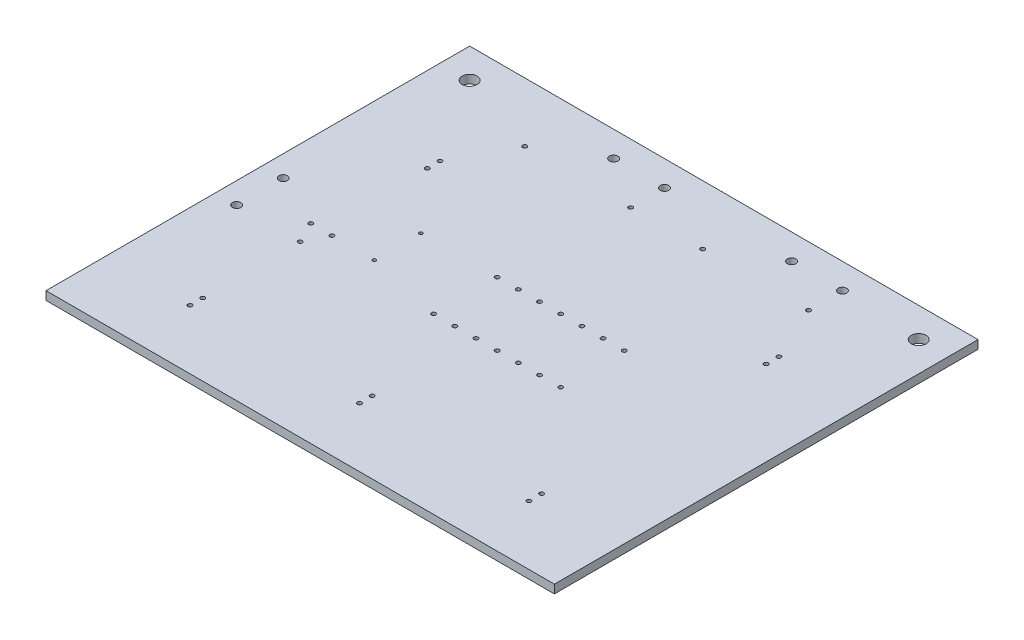
SolidWorks part; units mm, degrees
ref_plane "Front" through (0, 0, 0) normal (0, 0, 1) x (1, 0, 0)
ref_plane "Top" through (0, 0, 0) normal (0, 1, 0) x (1, 0, 0)
ref_plane "Right" through (0, 0, 0) normal (1, 0, 0) x (0, 0, -1)
sketch "Sketch1" plane through (0, 0, 0) normal (0, 1, 0) x (1, 0, 0)
  line L0 (0, 0) -> (0, 50)
  line L1 (0, 50) -> (60, 50)
  line L2 (60, 50) -> (60, 0)
  line L3 (60, 0) -> (0, 0)
  dimension "D1" = 60
  dimension "D2" = 50
extrude "Boss-Extrude1" add sketch "Sketch1" along normal blind 1
sketch "Sketch2" plane through (0, 1, 0) normal (0, 1, 0) x (1, 0, 0)
  line L0 (0, 50) -> (0, 0) construction
  line L1 (0, 0) -> (60, 0) construction
  circle A0 centre (10, 7) radius 0.25
  dimension "D1" = 0.5
  dimension "D2" = 10
  dimension "D3" = 7
extrude "Cut-Extrude1" cut sketch "Sketch2" against normal blind 1.5
pattern_linear "LPattern1" count 3 spacing 20 along (1, 0, 0) of "Cut-Extrude1"
sketch "Sketch3" plane through (0, 1, 0) normal (0, 1, 0) x (1, 0, 0)
  line L0 (0, 50) -> (0, 0) construction
  line L1 (0, 0) -> (60, 0) construction
  circle A0 centre (10, 8.5) radius 0.25
  dimension "D1" = 0.5
  dimension "D2" = 10
  dimension "D3" = 8.5
extrude "Cut-Extrude2" cut sketch "Sketch3" against normal blind 1.5
pattern_linear "LPattern2" count 3 spacing 20 along (1, 0, 0) of "Cut-Extrude2"
sketch "Sketch4" plane through (0, 1, 0) normal (0, 1, 0) x (1, 0, 0)
  line L0 (0, 0) -> (60, 0) construction
  line L1 (0, 50) -> (0, 0) construction
  circle A0 centre (2.5, 20) radius 0.5
  circle A1 centre (2.5, 25.5) radius 0.5
  dimension "D1" = 1
  dimension "D2" = 1
  dimension "D3" = 20
  dimension "D4" = 5.5
  dimension "D5" = 2.5
extrude "Cut-Extrude3" cut sketch "Sketch4" against normal blind 1.5
sketch "Sketch5" plane through (0, 1, 0) normal (0, 1, 0) x (1, 0, 0)
  line L0 (0, 0) -> (60, 0) construction
  line L1 (0, 50) -> (0, 0) construction
  line L2 (8.75, 22.5) -> (11.25, 22.5) construction
  circle A0 centre (10, 20) radius 0.25
  circle A1 centre (11.25, 22.5) radius 0.25
  circle A2 centre (8.75, 22.5) radius 0.25
  point P10 (10, 22.5)
  dimension "D1" = 0.5
  dimension "D2" = 0.5
  dimension "D3" = 0.5
  dimension "D4" = 20
  dimension "D5" = 10
  dimension "D6" = 2.5
  dimension "D7" = 2.5
extrude "Cut-Extrude4" cut sketch "Sketch5" against normal blind 1.5
sketch "Sketch6" plane through (0, 1, 0) normal (0, 1, 0) x (1, 0, 0)
  line L0 (0, 0) -> (60, 0) construction
  line L1 (0, 50) -> (0, 0) construction
  circle A0 centre (16.25, 22.5) radius 0.2
  circle A1 centre (16.25, 28) radius 0.2
  dimension "D1" = 0.4
  dimension "D2" = 0.4
  dimension "D3" = 22.5
  dimension "D4" = 16.25
  dimension "D5" = 5.5
extrude "Cut-Extrude5" cut sketch "Sketch6" against normal blind 1.5
sketch "Sketch7" plane through (0, 1, 0) normal (0, 1, 0) x (1, 0, 0)
  line L0 (0, 50) -> (0, 0) construction
  line L1 (0, 0) -> (60, 0) construction
  circle A0 centre (25.25, 28) radius 0.25
  circle A1 centre (25.25, 20.5) radius 0.25
  dimension "D1" = 0.5
  dimension "D4" = 0.5
  dimension "D2" = 25.25
  dimension "D3" = 28
  dimension "D5" = 7.5
extrude "Cut-Extrude6" cut sketch "Sketch7" against normal blind 1.5
pattern_linear "LPattern3" count 7 spacing 2.5 along (1, 0, 0) of "Cut-Extrude6"
sketch "Sketch8" plane through (0, 1, 0) normal (0, 1, 0) x (1, 0, 0)
  line L0 (60, 0) -> (60, 50) construction
  line L1 (60, 50) -> (0, 50) construction
  circle A0 centre (50, 35) radius 0.25
  circle A1 centre (50, 36.5) radius 0.25
  dimension "D1" = 0.5
  dimension "D2" = 0.5
  dimension "D3" = 10
  dimension "D4" = 13.5
  dimension "D5" = 1.5
extrude "Cut-Extrude7" cut sketch "Sketch8" against normal blind 1.5
sketch "Sketch9" plane through (0, 1, 0) normal (0, 1, 0) x (1, 0, 0)
  line L0 (60, 50) -> (0, 50) construction
  line L1 (60, 0) -> (60, 50) construction
  line L2 (0, 50) -> (0, 0) construction
  circle A0 centre (56.5, 46.5) radius 0.875
  circle A1 centre (3.5, 46.5) radius 0.875
  dimension "D1" = 1.75
  dimension "D4" = 1.75
  dimension "D2" = 3.5
  dimension "D3" = 3.5
  dimension "D5" = 3.5
  dimension "D6" = 3.5
extrude "Cut-Extrude8" cut sketch "Sketch9" against normal blind 1.5
sketch "Sketch10" plane through (0, 1, 0) normal (0, 1, 0) x (1, 0, 0)
  line L0 (60, 0) -> (60, 50) construction
  line L1 (60, 50) -> (0, 50) construction
  line L2 (0, 50) -> (0, 0) construction
  circle A0 centre (47, 47) radius 0.5
  circle A1 centre (41, 47) radius 0.5
  circle A2 centre (26, 47) radius 0.5
  circle A3 centre (20, 47) radius 0.5
  dimension "D1" = 1
  dimension "D4" = 1
  dimension "D7" = 1
  dimension "D8" = 1
  dimension "D2" = 13
  dimension "D3" = 3
  dimension "D5" = 6
  dimension "D6" = 6
  dimension "D9" = 3
  dimension "D10" = 26
extrude "Cut-Extrude9" cut sketch "Sketch10" against normal blind 1.5
sketch "Sketch11" plane through (0, 1, 0) normal (0, 1, 0) x (1, 0, 0)
  line L0 (60, 50) -> (0, 50) construction
  line L1 (60, 0) -> (60, 50) construction
  line L2 (0, 50) -> (0, 0) construction
  circle A0 centre (47, 43) radius 0.25
  circle A1 centre (34.5, 43) radius 0.25
  circle A2 centre (26, 43) radius 0.25
  circle A3 centre (13.5, 43) radius 0.25
  dimension "D1" = 0.5
  dimension "D2" = 0.5
  dimension "D3" = 0.5
  dimension "D4" = 0.5
  dimension "D5" = 7
  dimension "D6" = 13
  dimension "D7" = 12.5
  dimension "D9" = 26
  dimension "D10" = 12.5
extrude "Cut-Extrude10" cut sketch "Sketch11" against normal blind 1.5
sketch "Sketch12" plane through (0, 1, 0) normal (0, 1, 0) x (1, 0, 0)
  line L0 (60, 50) -> (0, 50) construction
  line L1 (0, 50) -> (0, 0) construction
  circle A0 centre (10, 36.5) radius 0.25
  circle A1 centre (10, 35) radius 0.25
  dimension "D1" = 0.5
  dimension "D2" = 0.5
  dimension "D3" = 1.5
  dimension "D4" = 13.5
  dimension "D5" = 10
extrude "Cut-Extrude11" cut sketch "Sketch12" against normal blind 1.5
